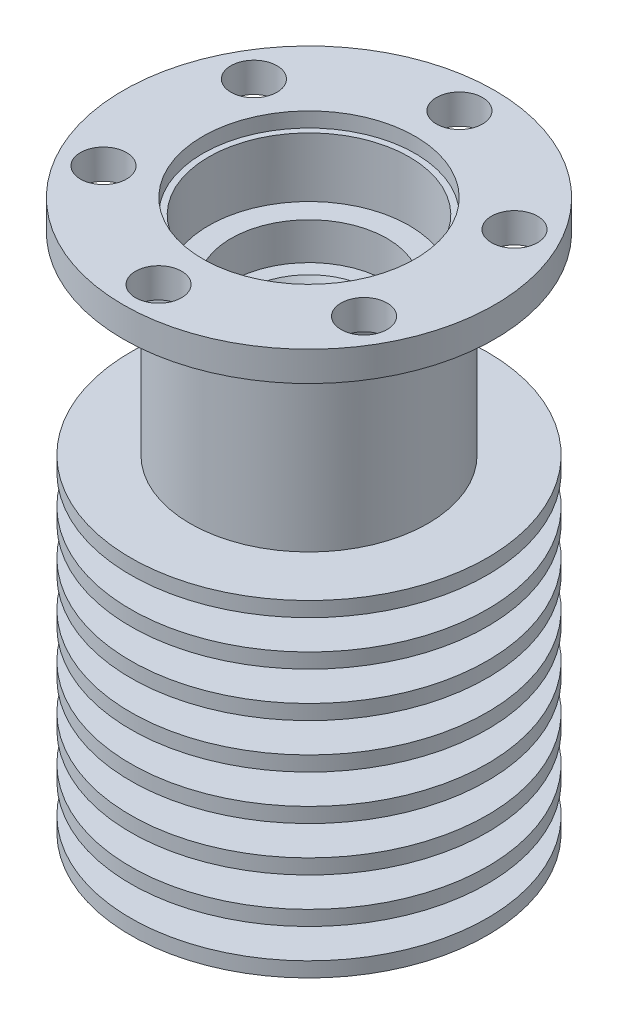
SolidWorks part; units mm, degrees
material "aluminio"
ref_plane "Alzado" through (0, 0, 0) normal (0, 0, 1) x (1, 0, 0)
ref_plane "Planta" through (0, 0, 0) normal (0, 1, 0) x (1, 0, 0)
ref_plane "Vista lateral" through (0, 0, 0) normal (1, 0, 0) x (0, 0, -1)
sketch "Croquis1" plane through (0, 0, 0) normal (0, 0, 1) x (1, 0, 0)
  line L0 (0, 0) -> (6, 0)
  line L1 (6, 0) -> (6, 9)
  line L2 (6, 9) -> (5.25, 9)
  line L3 (5.25, 9) -> (5.25, 12)
  line L4 (5.25, 12) -> (4.75, 12)
  line L5 (4.75, 12) -> (4.75, 22)
  line L6 (8, 35) -> (12.5, 35)
  line L7 (0, 37) -> (0, 0)
  line L8 (12.5, 35) -> (12.5, 37)
  line L9 (12.5, 37) -> (0, 37)
  line L12 (4.75, 22) -> (8, 22)
  line L13 (8, 22) -> (8, 35)
  line L19 (0, 37) -> (0, 0) construction
  dimension "D1" = 9
  dimension "D2" = 3
  dimension "D3" = 10
  dimension "D4" = 2
  dimension "D5" = 12.5
  dimension "D7" = 13
  dimension "D8" = 6
  dimension "D9" = 5.25
  dimension "D10" = 4.75
  dimension "D14" = 8
revolve "Revolución1" add sketch "Croquis1" angle 360 about L19
sketch "Croquis2" plane through (0, 0, 0) normal (0, 0, 1) x (1, 0, 0)
  line L0 (0, 0) -> (0, 37) construction
  line L2 (0, 0) -> (2.5, 0)
  line L3 (2.5, 0) -> (2.5, 12)
  line L4 (2.5, 12) -> (1.7, 12)
  line L5 (1.7, 12) -> (1.7, 14)
  line L6 (1.7, 14) -> (3.25, 14)
  line L7 (3.25, 14) -> (3.25, 29.5)
  line L8 (3.25, 29.5) -> (5.25, 29.5)
  line L9 (5.25, 29.5) -> (5.25, 32)
  line L10 (12.5, 37) -> (-12.5, 37) construction
  line L11 (0, 37) -> (6.75, 37)
  line L12 (5.25, 32) -> (6.75, 32)
  line L13 (6.75, 32) -> (6.75, 37)
  line L14 (0, 37) -> (0, 0)
  dimension "D1" = 12
  dimension "D2" = 2
  dimension "D3" = 5
  dimension "D5" = 2.5
  dimension "D6" = 13.5
  dimension "D8" = 10.5
  dimension "D9" = 6.5
  dimension "D10" = 3.4
  dimension "D11" = 5
revolve "Cortar-Revolución1" cut sketch "Croquis2" angle 360 about L0
cosmetic thread "Rosca cosmética1" parameters "D1"=10, "D2"=6
sketch "Croquis3" plane through (0, 0, 0) normal (0, -1, 0) x (1, 0, 0)
  circle A0 centre (0, 0) radius 3.25
  circle A1 centre (0, 0) radius 12
  dimension "D1" = 24
  dimension "D2" = 6.5
extrude "Saliente-Extruir1" add sketch "Croquis3" against normal blind 1
sketch "Croquis4" plane through (0, 0, 0) normal (0, 0, 1) x (1, 0, 0)
  line L0 (0, 0) -> (0, 36.9563) construction
pattern_linear "MatrizL1" count 8 spacing 3 along (0, 1, 0) of "Saliente-Extruir1"
sketch "Croquis5" plane through (0, 37, 0) normal (0, 1, 0) x (1, 0, 0)
  circle A0 centre (0, 0) radius 10.125 construction
  circle A1 centre (0, 10.125) radius 1.55
  dimension "D1" = 20.25
  dimension "D2" = 3.1
extrude "Cortar-Extruir1" cut sketch "Croquis5" against normal up to next (2 mm away)
pattern_circular "MatrizC1" count 6 over 360 about axis through (0, 0, 0) along (0, 1, 0) of "Cortar-Extruir1"
chamfer "Chaflán3" distance 0.3 angle 60 1 edges at (0, 14, -1.7)
sketch "Croquis6" plane through (0, 37, 0) normal (0, 1, 0) x (1, 0, 0)
  circle A0 centre (0, 0) radius 7.15
  dimension "D1" = 14.3
extrude "Cortar-Extruir2" cut sketch "Croquis6" against normal blind 1
chamfer "Chaflán2" distance 0.15 angle 60 1 edges at (0, 12, -1.7)
chamfer "Chaflán4" distance 1 angle 60 1 edges at (0, 29.5, -3.25)
